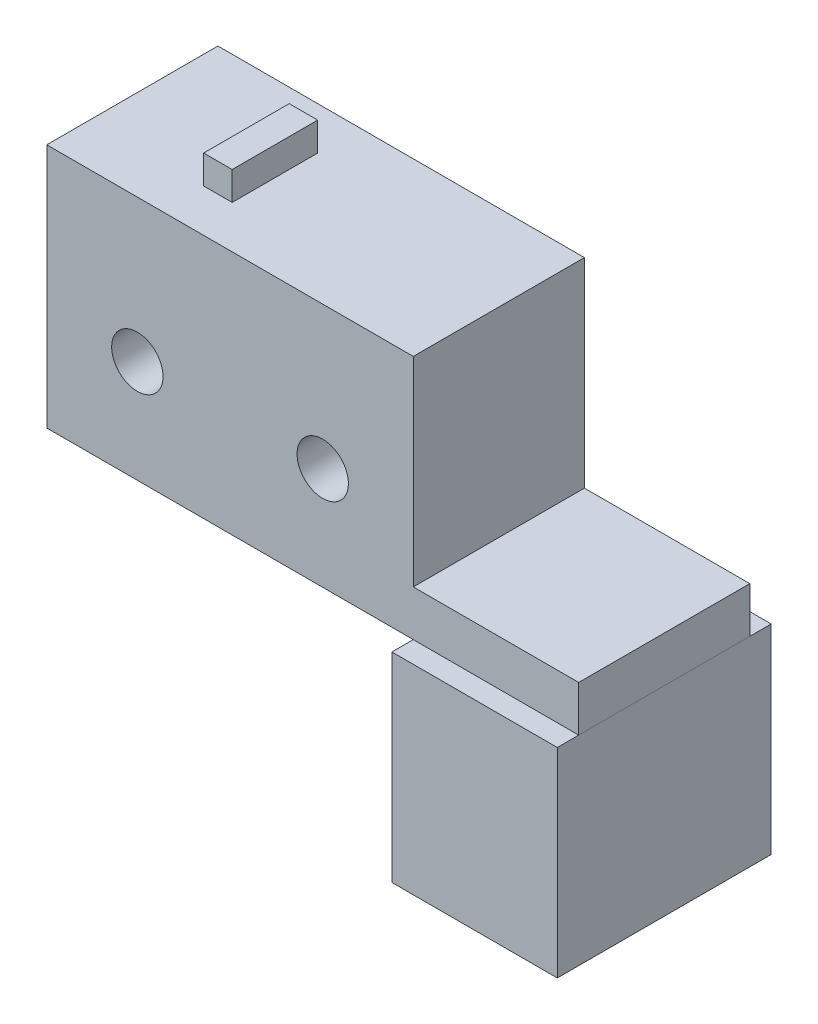
SolidWorks part; units mm, degrees
ref_plane "Front Plane" through (0, 0, 0) normal (0, 0, 1) x (1, 0, 0)
ref_plane "Top Plane" through (0, 0, 0) normal (0, 1, 0) x (1, 0, 0)
ref_plane "Right Plane" through (0, 0, 0) normal (1, 0, 0) x (0, 0, -1)
sketch "Sketch1" plane through (0, 0, 0) normal (0, 0, 1) x (1, 0, 0)
  line L0 (0, 0) -> (50000, 0) construction
  line L1 (-7, 20) -> (7, 20)
  line L2 (-9, 18) -> (-9, 2)
  line L3 (-7, 0) -> (7, 0)
  line L4 (9, 18) -> (9, 2)
  line L5 (0, 0) -> (0, 50000) construction
  circle A0 centre (7, 5) radius 1.5
  circle A1 centre (-7, 5) radius 1.5
  arc A2 (-7, 20) -> (-9, 18) centre (-7, 18) ccw
  arc A3 (7, 20) -> (9, 18) centre (7, 18) cw
  arc A4 (7, 0) -> (9, 2) centre (7, 2) ccw
  arc A5 (-9, 2) -> (-7, 0) centre (-7, 2) ccw
  point P15 (-9, 20)
  point P18 (9, 20)
  point P21 (9, 0)
  dimension "D5" = 3
  dimension "D3" = 14
  dimension "D4" = 5
  dimension "D6" = 2
  dimension "D1" = 18
  dimension "D2" = 20
extrude "Boss-Extrude1" add sketch "Sketch1" along normal blind 1.6
sketch "Sketch2" plane through (0, 0, 1.6) normal (0, 0, 1) x (1, 0, 0)
  line L2 (7, 20) -> (-7, 20) construction
  line L3 (7, 20) -> (-5.85, 20)
  line L4 (7, 20) -> (7, 10)
  line L5 (7, 10) -> (-5.85, 10)
  line L6 (-5.85, 20) -> (-5.85, 10)
  line L7 (9, 2) -> (9, 18) construction
  line M5 (7, 20) -> (-7, 20)
  dimension "D2" = 12.85
  dimension "D3" = 10
  dimension "D4" = 2
extrude "Boss-Extrude2" add sketch "Sketch2" along normal blind 6 contours L6 L5 L4 M5
sketch "Sketch3" plane through (0, 0, 7.6) normal (0, 0, 1) x (1, 0, 0)
  line L0 (7, 10) -> (-5.85, 10) construction
  line L1 (-5.85, 10) -> (7, 10)
  line L2 (-5.85, 10) -> (-5.85, 13)
  line L3 (-5.85, 13) -> (7, 13)
  line L4 (7, 10) -> (7, 13)
  line L5 (-5.85, 20) -> (-5.85, 10) construction
  line L6 (7, 20) -> (7, 10) construction
  dimension "D1" = 3
extrude "Cut-Extrude1" cut sketch "Sketch3" against normal blind 3
sketch "Sketch4" plane through (0, 0, 4.6) normal (0, 0, 1) x (1, 0, 0)
  line L0 (7, 11.5) -> (5, 11.5)
  line L1 (7, 10) -> (7, 13) construction
  line L2 (-5.85, 11.5) -> (-3.85, 11.5)
  line L3 (-5.85, 13) -> (-5.85, 10) construction
  line L4 (7, 13) -> (-5.85, 13) construction
  line L5 (-3.85, 13) -> (-0.425, 13)
  line L6 (-3.85, 13) -> (-3.85, 10)
  line L7 (-3.85, 10) -> (-0.425, 10)
  line L8 (-0.425, 13) -> (-0.425, 10)
  line L9 (-5.85, 10) -> (7, 10) construction
  line L11 (5, 13) -> (1.575, 13)
  line L12 (5, 13) -> (5, 10)
  line L13 (5, 10) -> (1.575, 10)
  line L14 (1.575, 13) -> (1.575, 10)
  line M2 (-5.85, 10) -> (7, 10)
  line M4 (7, 13) -> (-5.85, 13)
  dimension "D1" = 2
  dimension "D2" = 2
  dimension "D3" = 3.425
  dimension "D4" = 3.425
extrude "Cut-Extrude3" cut sketch "Sketch4" against normal blind 3 contours L14 L12 M4 M2 | L8 L6 M4 M2
sketch "Sketch5" plane through (7, 0, 0) normal (1, 0, 0) x (0, 0, -1)
  line L0 (-4.2467, 10.75) -> (-1.6, 10.75)
  line L1 (-4.6, 13) -> (-7.6, 13) construction
  line L5 (-1.6, 20) -> (-1.6, 10) construction
  line L7 (-3.85, 13) -> (-1.6, 13)
  line L8 (-3.85, 13) -> (-3.85, 10.75)
  line L9 (-3.85, 10.75) -> (-1.6, 10.75)
  line L10 (-1.6, 13) -> (-1.6, 10.75)
  line M4 (-1.6, 10) -> (-1.6, 20)
  dimension "D1" = 2.25
extrude "Cut-Extrude4" cut sketch "Sketch5" against normal through all contours L7 L8 L0 M4
sketch "Sketch10" plane through (0, 0, 7.6) normal (0, 0, 1) x (1, 0, 0)
  line L0 (-5.85, 20) -> (6.995, 23.2622)
  line L2 (-5.45, 20) -> (6.995, 23.1606)
  line L3 (7, 20) -> (-5.85, 20) construction
  line L4 (-5.85, 20) -> (-5.45, 20)
  line L5 (6.995, 23.2622) -> (6.995, 23.1606)
  line L6 (-5.85, 20) -> (-5.45, 20)
  dimension "D1" = 0.4
  dimension "D2" = 14.25
  dimension "D3" = 12.445
extrude "Boss-Extrude4" add sketch "Sketch10" against normal blind 4.75
sketch "Sketch11" plane through (0, 20, 0) normal (0, 1, 0) x (1, 0, 0)
  line L0 (-5.85, -7.6) -> (-5.85, -2.85) construction
  line L1 (7, -7.6) -> (-5.85, -7.6)
  line L2 (7, -7.6) -> (7, 2.4)
  line L3 (7, 2.4) -> (-5.85, 2.4)
  line L4 (-5.85, -7.6) -> (-5.85, 2.4)
  dimension "D1" = 10
extrude "Cut-Extrude8" cut sketch "Sketch11" along normal blind 4.75
sketch "草图1" plane through (0, 0, 1.6) normal (0, 0, 1) x (1, 0, 0)
  line L0 (-7, 0) -> (7, 0) construction
  line L1 (-6, 5) -> (4, 5)
  line L2 (-6, 5) -> (-6, -2)
  line L3 (-6, -2) -> (4, -2)
  line L4 (4, 5) -> (4, -2)
  line L5 (9, 2) -> (9, 18) construction
  dimension "D1" = 10
  dimension "D2" = 7
  dimension "D3" = 2
  dimension "D4" = 5
extrude "凸台-拉伸1" add sketch "草图1" along normal blind 5.8
sketch "草图3" plane through (-9, 0, 0) normal (-1, 0, 0) x (0, 0, 1)
  line L0 (1.6, 18) -> (1.6, 10.75)
  line L1 (1.6, 18) -> (1.6, 2) construction
  line L2 (1.6, 10.75) -> (10.367, 10.75)
  line L3 (10.367, 10.75) -> (10.367, -5.8822)
  line L4 (10.367, -5.8822) -> (-1.7521, -5.8822)
  line L5 (-1.7521, -5.8822) -> (-1.7521, 20.9312)
  line L6 (-1.7521, 20.9312) -> (1.6, 20.9312)
  line L7 (1.6, 20.9312) -> (1.6, 18)
  line L8 (3.85, 10.75) -> (1.6, 10.75) construction
extrude "切除-拉伸1" cut sketch "草图3" against normal through all
sketch "草图4" plane through (0, 0, 7.6) normal (0, 0, 1) x (1, 0, 0)
  line L0 (7, 20) -> (-5.85, 20) construction
  line L1 (0.575, 26.5197) -> (0.575, 6.3866) construction
  line L2 (-5.85, 20) -> (-5.85, 13) construction
  line L3 (7, 20) -> (7, 13) construction
  circle A0 centre (-2.675, 15) radius 0.9
  circle A1 centre (3.825, 15) radius 0.9
  dimension "D1" = 1.8
  dimension "D2" = 6.5
  dimension "D3" = 5
extrude "切除-拉伸2" cut sketch "草图4" against normal through all
sketch "草图5" plane through (0, 13, 0) normal (0, -1, 0) x (1, 0, 0)
  line L0 (12.8, 1.6) -> (12.8, 7.6)
  line L1 (12.8, 1.6) -> (-5.85, 1.6)
  line L2 (-5.85, 1.6) -> (-5.85, 7.6)
  line L3 (-5.85, 7.6) -> (12.8, 7.6)
  line L5 (-5.85, 4.6) -> (-5.85, 7.6) construction
  line L6 (7, 4.6) -> (7, 7.6) construction
  dimension "D1" = 5.8
extrude "凸台-拉伸3" add sketch "草图5" along normal blind 1.6
sketch "草图6" plane through (0, 11.4, 0) normal (0, -1, 0) x (1, 0, 0)
  line L0 (7, 8.35) -> (7, 0.85)
  line L1 (7, 0.85) -> (12.8, 0.85)
  line L2 (12.8, 0.85) -> (12.8, 8.35)
  line L3 (12.8, 8.35) -> (7, 8.35)
  line L5 (12.8, 1.6) -> (12.8, 7.6) construction
  line L6 (12.8, 7.6) -> (-5.85, 7.6) construction
  dimension "D1" = 5.8
  dimension "D2" = 7.5
  dimension "D3" = 0.75
extrude "凸台-拉伸4" add sketch "草图6" along normal blind 7 separate body
sketch "草图2" plane through (0, 20, 0) normal (0, 1, 0) x (1, 0, 0)
  line L0 (-1.85, -3.1) -> (-1.85, -6.1)
  line L1 (-1.85, -6.1) -> (-0.85, -6.1)
  line L2 (-0.85, -6.1) -> (-0.85, -3.1)
  line L3 (-0.85, -3.1) -> (-1.85, -3.1)
  line L6 (7, -1.6) -> (-5.85, -1.6) construction
  line L7 (-5.85, -7.6) -> (-5.85, -1.6) construction
  dimension "D1" = 3
  dimension "D2" = 1.5
  dimension "D3" = 1
  dimension "D4" = 4
extrude "凸台-拉伸2" add sketch "草图2" along normal blind 1
shell "抽壳1" thickness 0.5
